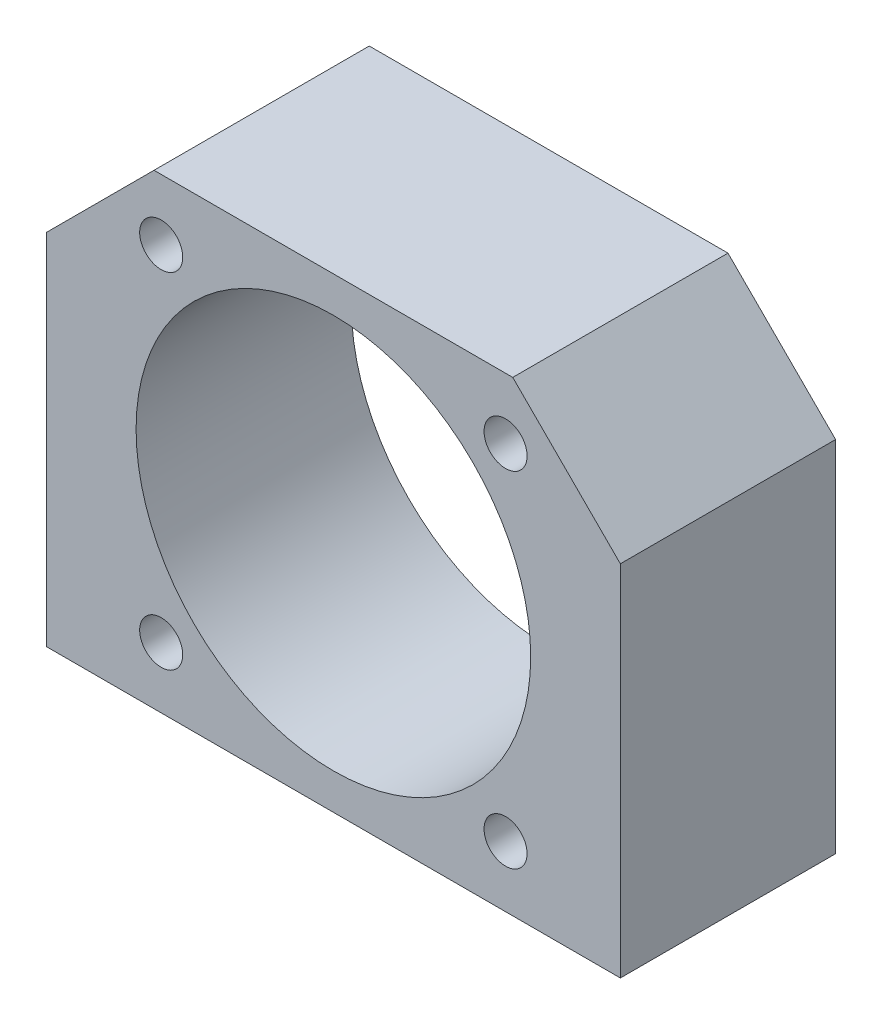
SolidWorks part; units mm, degrees
ref_plane "Płaszczyzna przednia" through (0, 0, 0) normal (0, 0, 1) x (1, 0, 0)
ref_plane "Płaszczyzna górna" through (0, 0, 0) normal (0, 1, 0) x (1, 0, 0)
ref_plane "Płaszczyzna prawa" through (0, 0, 0) normal (1, 0, 0) x (0, 0, -1)
sketch "Szkic1" plane through (0, 0, 0) normal (0, 0, 1) x (1, 0, 0)
  line L0 (40, 32.5) -> (-40, -32.5) construction
  line L1 (-40, 32.5) -> (40, 32.5)
  line L2 (-40, 32.5) -> (-40, -32.5)
  line L3 (-40, -32.5) -> (40, -32.5)
  line L4 (40, 32.5) -> (40, -32.5)
  line L5 (-40, 32.5) -> (40, -32.5) construction
  point P4 (0, 0)
  dimension "D1" = 80
  dimension "D2" = 65
extrude "Dodanie-wyciągnięcie1" add sketch "Szkic1" along normal blind 30
sketch "Szkic2" plane through (0, 0, 30) normal (0, 0, 1) x (1, 0, 0)
  line L0 (40, 32.5) -> (-40, 32.5) construction
  line L1 (40, -32.5) -> (40, 32.5) construction
  circle A0 centre (0, 0) radius 27.5
  dimension "D1" = 32.5
  dimension "D3" = 55
  dimension "D2" = 40
extrude "Wytnij-wyciągnięcie1" cut sketch "Szkic2" against normal blind 30
sketch "Szkic4" plane through (0, 0, 30) normal (0, 0, 1) x (1, 0, 0)
  circle A0 centre (-24, 24) radius 3
  circle A1 centre (24, 24) radius 3
  circle A2 centre (-24, -24) radius 3
  circle A3 centre (24, -24) radius 3
  dimension "D1" = 48
  dimension "D5" = 6
  dimension "D6" = 6
  dimension "D7" = 6
  dimension "D8" = 6
  dimension "D2" = 48
  dimension "D3" = 24
  dimension "D4" = 24
extrude "Wytnij-wyciągnięcie2" cut sketch "Szkic4" against normal blind 30
chamfer "Sfazowanie1" distance 15 angle 45 2 edges at (-40, 32.5, 15) (40, 32.5, 15)
sketch "Szkic6" plane through (0, -32.5, 0) normal (0, -1, 0) x (1, 0, 0)
  line L4 (-40, 30) -> (40, 30) construction
  line L5 (-40, 30) -> (-40, 0) construction
  line L7 (-40, 0) -> (40, 0) construction
  line L8 (40, 30) -> (40, 0) construction
  circle A0 centre (-33, 23) radius 3
  circle A1 centre (33, 23) radius 3
  circle A2 centre (33, 7) radius 3
  circle A3 centre (-33, 7) radius 3
  dimension "D1" = 7
  dimension "D6" = 6
  dimension "D2" = 7
  dimension "D3" = 7
  dimension "D4" = 7
  dimension "D5" = 7
extrude "Wytnij-wyciągnięcie3" cut sketch "Szkic6" against normal blind 25
sketch "Szkic8" plane through (0, 0, 0) normal (0, 0, -1) x (-1, 0, 0)
  circle A0 centre (24, -24) radius 5
  circle A1 centre (-24, -24) radius 5
  circle A2 centre (-24, 24) radius 5
  circle A3 centre (24, 24) radius 5
  dimension "D1" = 10
  dimension "D2" = 10
  dimension "D3" = 10
  dimension "D4" = 10
extrude "Wytnij-wyciągnięcie5" cut sketch "Szkic8" against normal blind 6
